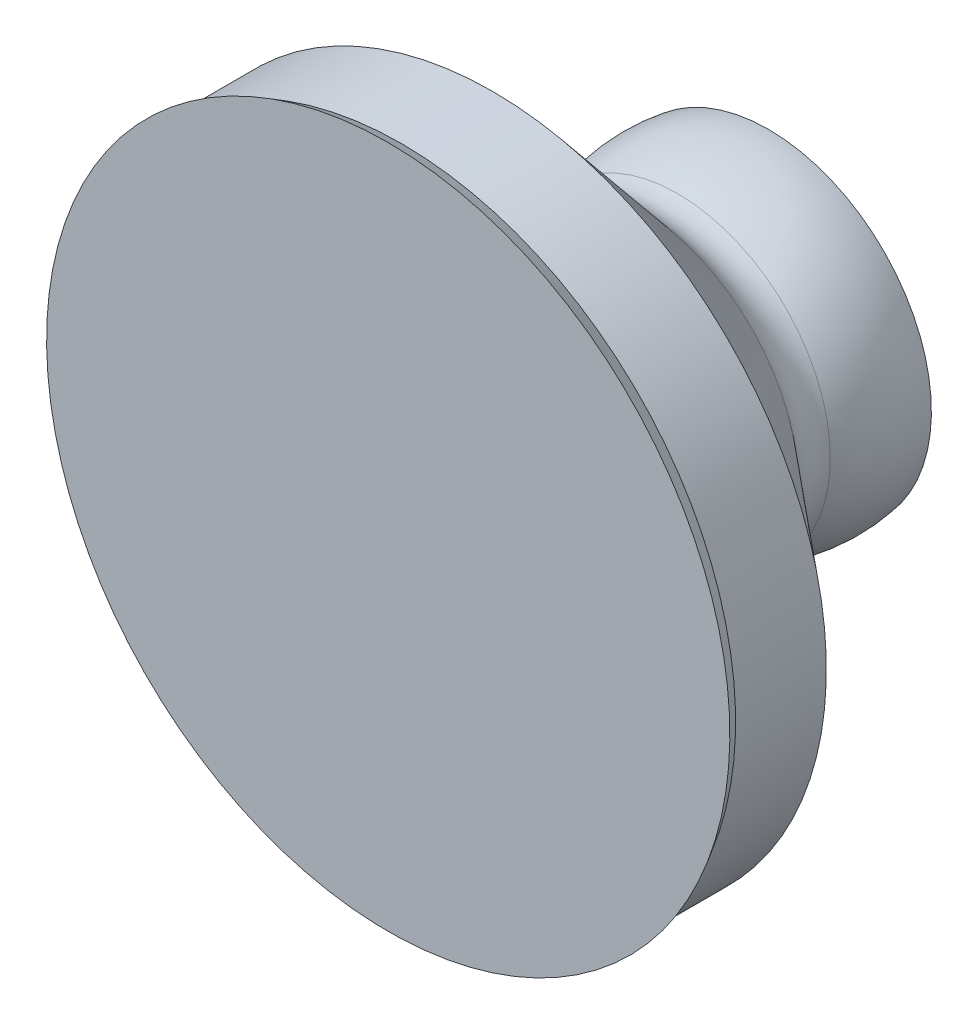
SolidWorks part; units mm, degrees
ref_plane "Front Plane" through (0, 0, 0) normal (0, 0, 1) x (1, 0, 0)
ref_plane "Top Plane" through (0, 0, 0) normal (0, 1, 0) x (1, 0, 0)
ref_plane "Right Plane" through (0, 0, 0) normal (1, 0, 0) x (0, 0, -1)
sketch "Sketch1" plane through (0, 0, 0) normal (1, 0, 0) x (0, 0, -1)
  line L0 (0, 0) -> (-50.9598, 0)
  line L2 (-50.9598, 34.2209) -> (-50.9598, 33.1794)
  line L6 (0, 35.8772) -> (0, 34.8622)
  line L7 (-24.752, 31.7091) -> (-24.752, 0) construction
  line L8 (0, 34.8622) -> (0, 0)
  line L9 (-50.9598, 33.1794) -> (-50.9598, 0) construction
  line L10 (-1.8421, 31.7091) -> (-37.0117, 31.7091) construction
  line L11 (-50.9598, 0) -> (-83.8211, 0)
  line L12 (-83.8211, 0) -> (-83.8211, 75.2821)
  line L13 (22.9099, 34.8622) -> (-36.6675, 34.8622) construction
  line L14 (-24.752, 31.7091) -> (-24.752, 32.7091) construction
  line L15 (-6.1471, 0) -> (0, 34.8622) construction
  line L16 (-41.1471, 0) -> (-50.9598, 34.2209) construction
  line L17 (-83.8211, 75.2821) -> (-80.8211, 73.55)
  line L18 (-80.8211, 73.55) -> (-60.8211, 73.55)
  line L19 (-60.8211, 73.55) -> (-29.225, 35.8952)
  line L20 (-41.1471, 0) -> (-28.9712, 33.4531) construction
  arc A0 (-28.9712, 33.4531) -> (-50.9598, 34.2209) centre (-41.1471, 0) ccw construction
  arc A1 (-19.6609, 32.7191) -> (0, 34.8622) centre (-6.1471, 0) cw
  arc A2 (-20.0427, 33.6433) -> (0, 35.8772) centre (-6.1471, 0) cw
  arc A3 (-28.9712, 33.4531) -> (-20.0427, 33.6433) centre (-24.752, 45.0454) ccw construction
  arc A4 (-50.9598, 33.1794) -> (-29.3132, 32.5134) centre (-41.1471, 0) cw construction
  arc A5 (-29.3132, 32.5134) -> (-24.752, 31.7091) centre (-24.752, 45.0454) ccw construction
  arc A7 (-24.752, 31.7091) -> (-19.6609, 32.7191) centre (-24.752, 45.0454) ccw construction
  arc A8 (-29.225, 35.8952) -> (-20.0427, 33.6433) centre (-23.0966, 41.0375) ccw
  point P9 (0, 0)
  point P10 (-6.1471, 35.4)
revolve "Revolve1" add sketch "Sketch1" angle 360 about L0
equation "\"Nominal_Diameter\"= 35mm"
equation "\"D1@Sketch1\"=\"Nominal_Diameter\" + 0.6mm"
equation "\"Wall_Thickness\"= 1mm"
equation "\"D5@Sketch1\"=\"Wall_Thickness\""
equation "\"D2@Sketch1\"=\"Nominal_Diameter\" + 0.4mm"
equation "\"D3@Sketch1\"=\"Nominal_Diameter\""
